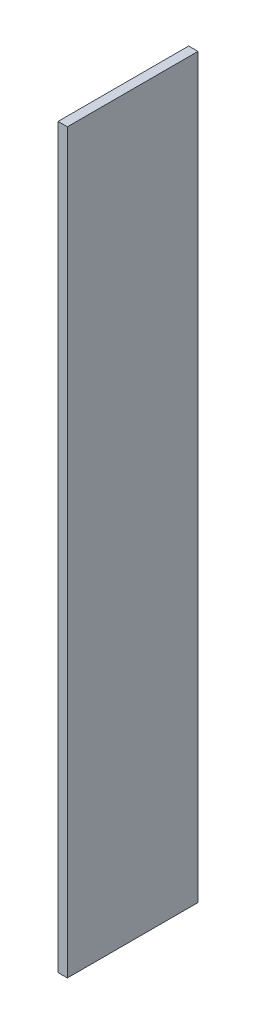
SolidWorks part; units mm, degrees
material "6061-T6 (SS)"
ref_plane "Front Plane" through (0, 0, 0) normal (0, 0, 1) x (1, 0, 0)
ref_plane "Top Plane" through (0, 0, 0) normal (0, 1, 0) x (1, 0, 0)
ref_plane "Right Plane" through (0, 0, 0) normal (1, 0, 0) x (0, 0, -1)
sketch "Sketch1" plane through (0, 0, 0) normal (1, 0, 0) x (0, 0, -1)
  line L1 (0, 0) -> (88.9, 0)
  line L2 (0, 0) -> (0, 501.65)
  line L3 (0, 501.65) -> (88.9, 501.65)
  line L4 (88.9, 0) -> (88.9, 501.65)
  dimension "D1" = 501.65
  dimension "D2" = 88.9
extrude "Boss-Extrude1" add sketch "Sketch1" along normal blind 6.35
